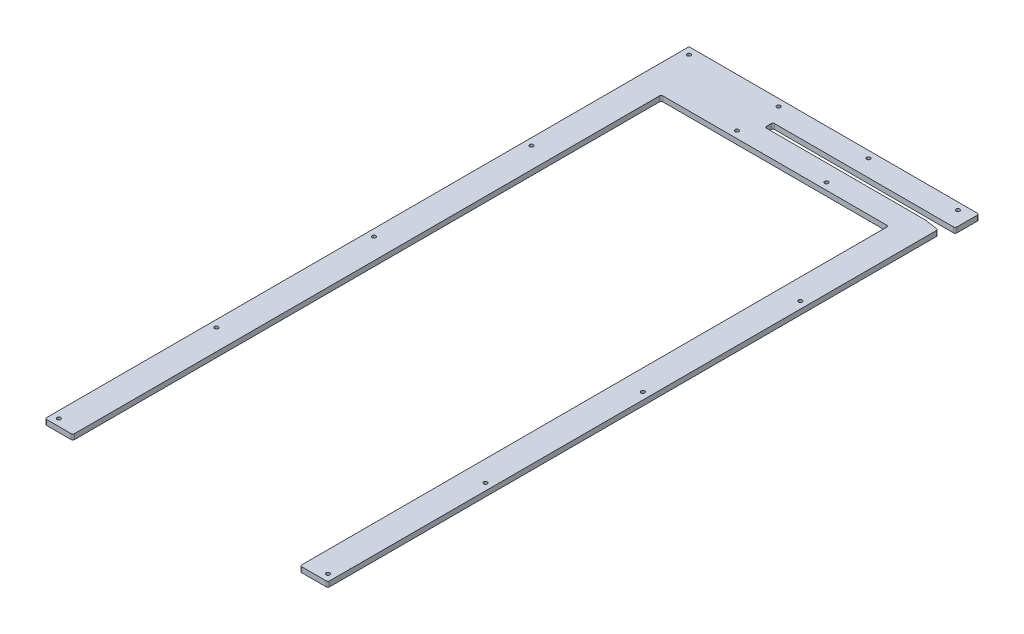
SolidWorks part; units mm, degrees
material "PE Low/Medium Density"
ref_plane "Front Plane" through (0, 0, 0) normal (0, 0, 1) x (1, 0, 0)
ref_plane "Top Plane" through (0, 0, 0) normal (0, 1, 0) x (1, 0, 0)
ref_plane "Right Plane" through (0, 0, 0) normal (1, 0, 0) x (0, 0, -1)
sketch "Sketch1" plane through (0, 0, 0) normal (0, 1, 0) x (1, 0, 0)
  line L0 (-258.3, 0) -> (-207.5, 0)
  line L1 (-207.5, 0) -> (-207.5, 1074.4)
  line L2 (-207.5, 1074.4) -> (207.5, 1074.4)
  line L3 (207.5, 1074.4) -> (207.5, 0)
  line L4 (207.5, 0) -> (258.3, 0)
  line L5 (258.3, 0) -> (258.3, 1113.9149)
  line L6 (230.3, 1117.85) -> (-61.7, 1117.85)
  line L7 (-61.7, 1117.85) -> (-61.7, 1132.55)
  line L8 (-61.7, 1132.55) -> (271.3, 1132.55)
  line L9 (271.3, 1132.55) -> (271.3, 1176)
  line L10 (271.3, 1176) -> (-258.3, 1176)
  line L11 (-258.3, 1176) -> (-258.3, 0)
  line L12 (-207.5, 0) -> (207.5, 0) construction
  line L13 (-182.147, 1176) -> (-182.147, 1074.4) construction
  line L14 (-61.7, 1125.2) -> (-162.228, 1125.2) construction
  line L15 (230.3, 1117.85) -> (258.3, 1113.9149)
  point P0 (0, 0)
  point P18 (-182.147, 1125.2)
  dimension "D1" = 516.6
  dimension "D2" = 1176
  dimension "D3" = 50.8
  dimension "D4" = 101.6
  dimension "D5" = 14.7
  dimension "D6" = 320
  dimension "D7" = 13
  dimension "D8" = 8
  dimension "D9" = 28
extrude "Boss-Extrude1" add sketch "Sketch1" along normal blind 9.525
sketch "Sketch4" [suppressed] plane through (0, 0, 0) normal (0, -1, 0) x (1, 0, 0)
  line L0 (271.3, -1176) -> (-258.3, -1176) construction
  line L1 (-258.3, -1176) -> (-207.5, -1176)
  line L2 (-258.3, -1176) -> (-258.3, -1376)
  line L3 (-258.3, -1376) -> (-207.5, -1376)
  line L4 (-207.5, -1176) -> (-207.5, -1376)
  line L5 (258.3, -1176) -> (207.5, -1176)
  line L6 (258.3, -1176) -> (258.3, -1376)
  line L7 (258.3, -1376) -> (207.5, -1376)
  line L8 (207.5, -1176) -> (207.5, -1376)
  line L9 (258.3, 0) -> (258.3, -1113.9149) construction
  line L10 (207.5, -1074.4) -> (207.5, 0) construction
  line L11 (-207.5, 0) -> (-207.5, -1074.4) construction
  dimension "D1" = 200
extrude "Boss-Extrude2" [suppressed] add sketch "Sketch4" against normal up to surface (9.525 mm away)
hole_wizard "CSK for 1/4 Flat Head Machine Screw (100)1" positions "Sketch3" profile "Sketch2" countersink size "1/4" standard "Ansi Inch" end condition through all
sketch "Sketch3" plane through (0, 0, 0) normal (0, -1, 0) x (1, 0, 0)
  line L0 (271.3, -1176) -> (-258.3, -1176) construction
  line L1 (-258.3, -1176) -> (-258.3, 0) construction
  point P0 (-245.6, -1163.3)
  dimension "D1" = 12.7
  dimension "D2" = 12.7
sketch "Sketch2" plane through (-245.6, 0, -1163.3) normal (1, 0, 0) x (0, 0, -1)
  line L0 (0, 0) -> (0, 9.525)
  line L1 (0, 9.525) -> (3.3782, 9.525)
  line L2 (3.3782, 9.525) -> (3.3782, 4.5682)
  line L3 (3.3782, 4.5682) -> (8.8224, 0)
  line L5 (8.8224, 0) -> (0, 0)
  line L6 (-3.3782, 4.5682) -> (-8.8224, 0) construction
  line L11 (0, -6.35) -> (0, 107.95) construction
  dimension "Thru Hole Dia." = 6.7564
  dimension "Thru Hole Depth" = 9.525
  dimension "Near C'Sink Dia." = 17.6448
  dimension "Near C'Sink Angle" = 100
pattern_linear "LPattern1" count 2 spacing 491.2 along (1, 0, 0) count 5 spacing 287.65 along (0, 0, 1) of "CSK for 1/4 Flat Head Machine Screw (100)1"
pattern_linear "LPattern2" count 3 spacing 163.7333 along (1, 0, 0) count 2 spacing 76.2 along (0, 0, 1) skipping (0, 1) of "CSK for 1/4 Flat Head Machine Screw (100)1"
hole_wizard "CSK for 1/4 Flat Head Machine Screw (100)2" positions "Sketch6" profile "Sketch5" countersink size "1/4" standard "Ansi Inch"
sketch "Sketch6" plane through (0, 0, 0) normal (0, -1, 0) x (1, 0, 0)
  line L0 (-258.3, -1376) -> (-207.5, -1376) construction
  line L1 (-258.3, -1376) -> (-258.3, 0) construction
  point P0 (-245.6, -1363.3)
  dimension "D1" = 12.7
  dimension "D2" = 12.7
sketch "Sketch5" plane through (-245.6, 0, -1363.3) normal (1, 0, 0) x (0, 0, -1)
  line L0 (0, 0) -> (0, 9.525)
  line L1 (0, 9.525) -> (3.3782, 9.525)
  line L2 (3.3782, 9.525) -> (3.3782, 4.5682)
  line L3 (3.3782, 4.5682) -> (8.8224, 0)
  line L5 (8.8224, 0) -> (0, 0)
  line L6 (-3.3782, 4.5682) -> (-8.8224, 0) construction
  line L11 (0, -6.35) -> (0, 107.95) construction
  dimension "Thru Hole Dia." = 6.7564
  dimension "Thru Hole Depth" = 9.5251
  dimension "Near C'Sink Dia." = 17.6448
  dimension "Near C'Sink Angle" = 100
mirror "Mirror1" [suppressed] about plane through (0, 0, 0) normal (1, 0, 0)
fillet "Fillet1" radius 3.175 11 edges at (258.3, 4.7625, 0) (207.5, 4.7625, 0) (-207.5, 4.7625, 0) (-258.3, 4.7625, 0) (207.5, 4.7625, -1074.4) (-207.5, 4.7625, -1074.4) (258.3, 4.7625, -1113.9149) (271.3, 4.7625, -1132.55) (271.3, 4.7625, -1176) (-61.7, 4.7625, -1117.85) (-61.7, 4.7625, -1132.55)
fillet "Fillet2" [suppressed] radius 3.175
